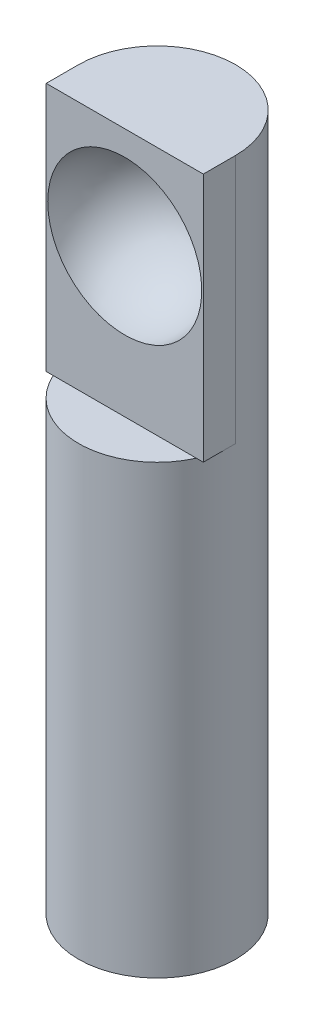
SolidWorks part; units mm, degrees
ref_plane "Front Plane" through (0, 0, 0) normal (0, 0, 1) x (1, 0, 0)
ref_plane "Top Plane" through (0, 0, 0) normal (0, 1, 0) x (1, 0, 0)
ref_plane "Right Plane" through (0, 0, 0) normal (1, 0, 0) x (0, 0, -1)
sketch "Sketch1" plane through (0, 0, 0) normal (0, 0, 1) x (1, 0, 0)
  line L1 (-2.55, -11.3) -> (2.55, -11.3)
  line L2 (-2.55, -11.3) -> (-2.55, 11.3)
  line L3 (-2.55, 11.3) -> (2.55, 11.3)
  line L4 (2.55, -11.3) -> (2.55, 11.3)
  line L5 (-2.55, -11.3) -> (2.55, 11.3) construction
  line L6 (-2.55, 11.3) -> (2.55, -11.3) construction
  point P0 (0, 0)
  dimension "D1" = 5.1
  dimension "D2" = 22.6
extrude "Boss-Extrude1" add sketch "Sketch1" along normal mid plane 5.1
sketch "Sketch3" plane through (0, 0, -2.55) normal (0, 0, -1) x (-1, 0, 0)
  line L1 (-2.55, 3.2) -> (2.55, 3.2)
  line L2 (-2.55, 3.2) -> (-2.55, 11.3)
  line L3 (-2.55, 11.3) -> (2.55, 11.3)
  line L4 (2.55, 3.2) -> (2.55, 11.3)
  line L5 (-2.55, 3.2) -> (2.55, 11.3) construction
  line L6 (-2.55, 11.3) -> (2.55, 3.2) construction
  point P0 (0, 7.25)
  point P6 (0, 11.3)
  dimension "D1" = 8.1
  dimension "D2" = 5.1
extrude "Boss-Extrude2" add sketch "Sketch3" along normal blind 1
sketch "Sketch4" plane through (0, -11.3, 0) normal (0, -1, 0) x (1, 0, 0)
  line L0 (-2.55, 2.55) -> (-2.55, -2.55) construction
  line L1 (-2.55, -2.55) -> (2.55, -2.55) construction
  line L2 (2.55, 2.55) -> (2.55, -2.55) construction
  line L3 (-2.55, 2.55) -> (2.55, 2.55) construction
  line L4 (-2.55, 2.55) -> (-2.55, -2.55)
  line L5 (-2.55, -2.55) -> (2.55, -2.55)
  line L6 (2.55, 2.55) -> (2.55, -2.55)
  line L7 (-2.55, 2.55) -> (2.55, 2.55)
  circle A0 centre (0, 0) radius 2.55
  line M1 (-2.55, -2.55) -> (2.55, -2.55)
  line M2 (2.55, -2.55) -> (2.55, 2.55)
  line M3 (2.55, 2.55) -> (-2.55, 2.55)
  line M4 (-2.55, 2.55) -> (-2.55, -2.55)
  dimension "D1" = 5.1
extrude "Cut-Extrude1" cut sketch "Sketch4" against normal up to surface (14.5 mm away) contours A0 L7 M4 | A0 L6 M3 | A0 L5 M2 | A0 L4 M1 up to face at (0, 3.2, -3.05)
sketch "Sketch5" plane through (0, 11.3, 0) normal (0, 1, 0) x (1, 0, 0)
  line L0 (-2.55, -2.55) -> (-2.55, 3.55) construction
  line L1 (2.55, -2.55) -> (-2.55, -2.55)
  line L2 (2.55, -2.55) -> (2.55, -1.05)
  line L3 (2.55, -1.05) -> (-2.55, -1.05)
  line L4 (-2.55, -2.55) -> (-2.55, -1.05)
  dimension "D1" = 1.5
extrude "Cut-Extrude2" cut sketch "Sketch5" against normal up to surface (8.1 mm away) up to face at (0, 3.2, -2.4125)
sketch "Sketch6" plane through (0, 0, 1.05) normal (0, 0, 1) x (1, 0, 0)
  line L0 (2.55, 11.3) -> (-2.55, 11.3) construction
  line L1 (-2.55, -11.3) -> (2.55, -11.3) construction
  line L2 (-2.5, 8) -> (2.5, 8) construction
  line L3 (-2.5, 8) -> (2.5, 8)
  arc A0 (-2.5, 8) -> (2.5, 8) centre (0, 8) ccw
  point P4 (0, 11.3)
  dimension "D1" = 5
  dimension "D2" = 19.3
revolve "Cut-Revolve2" cut sketch "Sketch6" angle 360 about L2
sketch "Sketch7" plane through (0, 3.2, 0) normal (0, -1, 0) x (1, 0, 0)
  line L0 (-2.55, -3.55) -> (-2.55, 0) construction
  line L1 (2.55, -3.55) -> (2.55, 0) construction
  line L3 (2.55, -3.55) -> (-2.55, -3.55) construction
  line L4 (2.55, -3.55) -> (2.55, 0)
  line L5 (2.55, -3.55) -> (-2.55, -3.55)
  line L6 (-2.55, -3.55) -> (-2.55, 0)
  arc A0 (-2.55, -1.95) -> (2.55, -1.95) centre (0, -0.3697) ccw
  line M1 (2.55, -3.55) -> (2.55, 0)
  line M4 (-2.55, -3.55) -> (2.55, -3.55)
  dimension "D1" = 3
  dimension "D2" = 3
extrude "Cut-Extrude3" cut sketch "Sketch7" against normal through all contours A0 L6 M4 | A0 M4 M1
